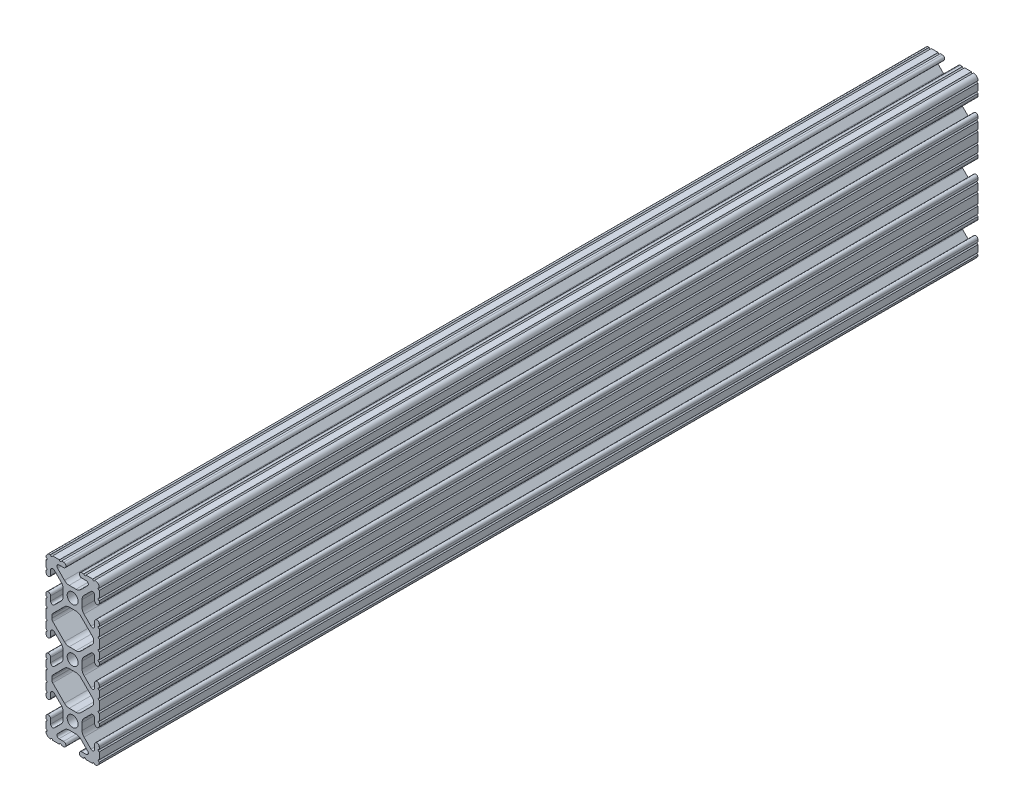
SolidWorks part; units mm, degrees
ref_plane "Front Plane" through (0, 0, 0) normal (0, 0, 1) x (1, 0, 0)
ref_plane "Top Plane" through (0, 0, 0) normal (0, 1, 0) x (1, 0, 0)
ref_plane "Right Plane" through (0, 0, 0) normal (1, 0, 0) x (0, 0, -1)
sketch "Sketch1" plane through (0, 0, 0) normal (0, 0, 1) x (1, 0, 0)
  line L0 (-9.9314, 12.1463) -> (-9.9314, 13.2537)
  line L1 (-9.4702, 14.3673) -> (-3.8759, 19.9616)
  line L2 (-1.6308, 20.8915) -> (1.6308, 20.8915)
  line L3 (3.8759, 19.9616) -> (9.4702, 14.3673)
  line L4 (9.9314, 13.2537) -> (9.9314, 12.1463)
  line L5 (9.4702, 11.0327) -> (3.8759, 5.4384)
  line L6 (1.6308, 4.5085) -> (-1.6308, 4.5085)
  line L7 (-3.8759, 5.4384) -> (-9.4702, 11.0327)
  line L8 (-9.9314, -13.2537) -> (-9.9314, -12.1463)
  line L9 (-9.4702, -11.0327) -> (-3.8759, -5.4384)
  line L10 (-1.6308, -4.5085) -> (1.6308, -4.5085)
  line L11 (3.8759, -5.4384) -> (9.4702, -11.0327)
  line L12 (9.9314, -12.1463) -> (9.9314, -13.2537)
  line L13 (9.4702, -14.3673) -> (3.8759, -19.9616)
  line L14 (1.6308, -20.8915) -> (-1.6308, -20.8915)
  line L15 (-3.8759, -19.9616) -> (-9.4702, -14.3673)
  line L16 (-6.3246, 38.1) -> (-9.5504, 38.1)
  line L17 (-12.7, 34.9504) -> (-12.7, 31.7246)
  line L18 (-12.7, 30.7086) -> (-12.7, 29.7023)
  line L19 (-10.4902, 29.7023) -> (-10.4902, 31.8748)
  line L20 (-8.7558, 32.5932) -> (-5.4384, 29.2759)
  line L21 (-4.5085, 27.0308) -> (-4.5085, 23.7692)
  line L22 (-5.4384, 21.5241) -> (-8.7558, 18.2068)
  line L23 (-10.4902, 18.9252) -> (-10.4902, 21.0977)
  line L24 (-12.7, 21.0977) -> (-12.7, 20.0914)
  line L25 (-12.7, 19.0754) -> (-12.7, 15.8496)
  line L26 (-12.7, 14.8336) -> (-12.7, 10.5664)
  line L27 (-12.7, 9.5504) -> (-12.7, 6.3246)
  line L28 (-12.7, 5.3086) -> (-12.7, 4.3023)
  line L29 (-10.4902, 4.3023) -> (-10.4902, 6.4748)
  line L30 (-8.7558, 7.1932) -> (-5.4384, 3.8759)
  line L31 (-4.5085, 1.6308) -> (-4.5085, -1.6308)
  line L32 (-5.4384, -3.8759) -> (-8.7558, -7.1932)
  line L33 (-10.4902, -6.4748) -> (-10.4902, -4.3023)
  line L34 (-12.7, -4.3023) -> (-12.7, -5.3086)
  line L35 (-12.7, -6.3246) -> (-12.7, -9.5504)
  line L36 (-12.7, -10.5664) -> (-12.7, -14.8336)
  line L37 (-12.7, -15.8496) -> (-12.7, -19.0754)
  line L38 (-12.7, -20.0914) -> (-12.7, -21.0977)
  line L39 (-10.4902, -21.0977) -> (-10.4902, -18.9252)
  line L40 (-8.7558, -18.2068) -> (-5.4384, -21.5241)
  line L41 (-4.5085, -23.7692) -> (-4.5085, -27.0308)
  line L42 (-5.4384, -29.2759) -> (-8.7558, -32.5932)
  line L43 (-10.4902, -31.8748) -> (-10.4902, -29.7023)
  line L44 (-12.7, -29.7023) -> (-12.7, -30.7086)
  line L45 (-12.7, -31.7246) -> (-12.7, -34.9504)
  line L46 (-9.5504, -38.1) -> (-6.3246, -38.1)
  line L47 (-5.3086, -38.1) -> (-4.3023, -38.1)
  line L48 (-4.3023, -35.8902) -> (-6.4748, -35.8902)
  line L49 (-7.1932, -34.1558) -> (-3.8759, -30.8384)
  line L50 (-1.6308, -29.9085) -> (1.6308, -29.9085)
  line L51 (3.8759, -30.8384) -> (7.1932, -34.1558)
  line L52 (6.4748, -35.8902) -> (4.3023, -35.8902)
  line L53 (4.3023, -38.1) -> (5.3086, -38.1)
  line L54 (6.3246, -38.1) -> (9.5504, -38.1)
  line L55 (12.7, -34.9504) -> (12.7, -31.7246)
  line L56 (12.7, -30.7086) -> (12.7, -29.7023)
  line L57 (10.4902, -29.7023) -> (10.4902, -31.8748)
  line L58 (8.7558, -32.5932) -> (5.4384, -29.2759)
  line L59 (4.5085, -27.0308) -> (4.5085, -23.7692)
  line L60 (5.4384, -21.5241) -> (8.7558, -18.2068)
  line L61 (10.4902, -18.9252) -> (10.4902, -21.0977)
  line L62 (12.7, -21.0977) -> (12.7, -20.0914)
  line L63 (12.7, -19.0754) -> (12.7, -15.8496)
  line L64 (12.7, -14.8336) -> (12.7, -10.5664)
  line L65 (12.7, -9.5504) -> (12.7, -6.3246)
  line L66 (12.7, -5.3086) -> (12.7, -4.3023)
  line L67 (10.4902, -4.3023) -> (10.4902, -6.4748)
  line L68 (8.7558, -7.1932) -> (5.4384, -3.8759)
  line L69 (4.5085, -1.6308) -> (4.5085, 1.6308)
  line L70 (5.4384, 3.8759) -> (8.7558, 7.1932)
  line L71 (10.4902, 6.4748) -> (10.4902, 4.3023)
  line L72 (12.7, 4.3023) -> (12.7, 5.3086)
  line L73 (12.7, 6.3246) -> (12.7, 9.5504)
  line L74 (12.7, 10.5664) -> (12.7, 14.8336)
  line L75 (12.7, 15.8496) -> (12.7, 19.0754)
  line L76 (12.7, 20.0914) -> (12.7, 21.0977)
  line L77 (10.4902, 21.0977) -> (10.4902, 18.9252)
  line L78 (8.7558, 18.2068) -> (5.4384, 21.5241)
  line L79 (4.5085, 23.7692) -> (4.5085, 27.0308)
  line L80 (5.4384, 29.2759) -> (8.7558, 32.5932)
  line L81 (10.4902, 31.8748) -> (10.4902, 29.7023)
  line L82 (12.7, 29.7023) -> (12.7, 30.7086)
  line L83 (12.7, 31.7246) -> (12.7, 34.9504)
  line L84 (9.5504, 38.1) -> (6.3246, 38.1)
  line L85 (5.3086, 38.1) -> (4.3023, 38.1)
  line L86 (4.3023, 35.8902) -> (6.4748, 35.8902)
  line L87 (7.1932, 34.1558) -> (3.8759, 30.8384)
  line L88 (1.6308, 29.9085) -> (-1.6308, 29.9085)
  line L89 (-3.8759, 30.8384) -> (-7.1932, 34.1558)
  line L90 (-6.4748, 35.8902) -> (-4.3023, 35.8902)
  line L91 (-4.3023, 38.1) -> (-5.3086, 38.1)
  circle A0 centre (0, 25.4) radius 2.6035
  arc A1 (-9.9314, 13.2537) -> (-9.4702, 14.3673) centre (-8.3566, 13.2537) cw
  arc A2 (-3.8759, 19.9616) -> (-1.6308, 20.8915) centre (-1.6308, 17.7165) cw
  arc A3 (1.6308, 20.8915) -> (3.8759, 19.9616) centre (1.6308, 17.7165) cw
  arc A4 (9.4702, 14.3673) -> (9.9314, 13.2537) centre (8.3566, 13.2537) cw
  arc A5 (9.9314, 12.1463) -> (9.4702, 11.0327) centre (8.3566, 12.1463) cw
  arc A6 (3.8759, 5.4384) -> (1.6308, 4.5085) centre (1.6308, 7.6835) cw
  arc A7 (-1.6308, 4.5085) -> (-3.8759, 5.4384) centre (-1.6308, 7.6835) cw
  arc A8 (-9.4702, 11.0327) -> (-9.9314, 12.1463) centre (-8.3566, 12.1463) cw
  arc A9 (-9.9314, -12.1463) -> (-9.4702, -11.0327) centre (-8.3566, -12.1463) cw
  arc A10 (-3.8759, -5.4384) -> (-1.6308, -4.5085) centre (-1.6308, -7.6835) cw
  arc A11 (1.6308, -4.5085) -> (3.8759, -5.4384) centre (1.6308, -7.6835) cw
  arc A12 (9.4702, -11.0327) -> (9.9314, -12.1463) centre (8.3566, -12.1463) cw
  arc A13 (9.9314, -13.2537) -> (9.4702, -14.3673) centre (8.3566, -13.2537) cw
  arc A14 (3.8759, -19.9616) -> (1.6308, -20.8915) centre (1.6308, -17.7165) cw
  arc A15 (-1.6308, -20.8915) -> (-3.8759, -19.9616) centre (-1.6308, -17.7165) cw
  arc A16 (-9.4702, -14.3673) -> (-9.9314, -13.2537) centre (-8.3566, -13.2537) cw
  circle A17 centre (0, -25.4) radius 2.6035
  circle A18 centre (0, 0) radius 2.6035
  arc A19 (-5.3086, 38.1) -> (-6.3246, 38.1) centre (-5.8166, 38.1) cw
  arc A20 (-9.5504, 38.1) -> (-10.5664, 38.1) centre (-10.0584, 38.1) cw
  arc A21 (-10.5664, 38.1) -> (-12.7, 35.9664) centre (-10.592, 35.992) ccw
  arc A22 (-12.7, 35.9664) -> (-12.7, 34.9504) centre (-12.7, 35.4584) cw
  arc A23 (-12.7, 31.7246) -> (-12.7, 30.7086) centre (-12.7, 31.2166) cw
  arc A24 (-12.7, 29.7023) -> (-10.4902, 29.7023) centre (-11.5951, 29.7023) ccw
  arc A25 (-10.4902, 31.8748) -> (-8.7558, 32.5932) centre (-9.4742, 31.8748) cw
  arc A26 (-5.4384, 29.2759) -> (-4.5085, 27.0308) centre (-7.6835, 27.0308) cw
  arc A27 (-4.5085, 23.7692) -> (-5.4384, 21.5241) centre (-7.6835, 23.7692) cw
  arc A28 (-8.7558, 18.2068) -> (-10.4902, 18.9252) centre (-9.4742, 18.9252) cw
  arc A29 (-10.4902, 21.0977) -> (-12.7, 21.0977) centre (-11.5951, 21.0977) ccw
  arc A30 (-12.7, 20.0914) -> (-12.7, 19.0754) centre (-12.7, 19.5834) cw
  arc A31 (-12.7, 15.8496) -> (-12.7, 14.8336) centre (-12.7, 15.3416) cw
  arc A32 (-12.7, 10.5664) -> (-12.7, 9.5504) centre (-12.7, 10.0584) cw
  arc A33 (-12.7, 6.3246) -> (-12.7, 5.3086) centre (-12.7, 5.8166) cw
  arc A34 (-12.7, 4.3023) -> (-10.4902, 4.3023) centre (-11.5951, 4.3023) ccw
  arc A35 (-10.4902, 6.4748) -> (-8.7558, 7.1932) centre (-9.4742, 6.4748) cw
  arc A36 (-5.4384, 3.8759) -> (-4.5085, 1.6308) centre (-7.6835, 1.6308) cw
  arc A37 (-4.5085, -1.6308) -> (-5.4384, -3.8759) centre (-7.6835, -1.6308) cw
  arc A38 (-8.7558, -7.1932) -> (-10.4902, -6.4748) centre (-9.4742, -6.4748) cw
  arc A39 (-10.4902, -4.3023) -> (-12.7, -4.3023) centre (-11.5951, -4.3023) ccw
  arc A40 (-12.7, -5.3086) -> (-12.7, -6.3246) centre (-12.7, -5.8166) cw
  arc A41 (-12.7, -9.5504) -> (-12.7, -10.5664) centre (-12.7, -10.0584) cw
  arc A42 (-12.7, -14.8336) -> (-12.7, -15.8496) centre (-12.7, -15.3416) cw
  arc A43 (-12.7, -19.0754) -> (-12.7, -20.0914) centre (-12.7, -19.5834) cw
  arc A44 (-12.7, -21.0977) -> (-10.4902, -21.0977) centre (-11.5951, -21.0977) ccw
  arc A45 (-10.4902, -18.9252) -> (-8.7558, -18.2068) centre (-9.4742, -18.9252) cw
  arc A46 (-5.4384, -21.5241) -> (-4.5085, -23.7692) centre (-7.6835, -23.7692) cw
  arc A47 (-4.5085, -27.0308) -> (-5.4384, -29.2759) centre (-7.6835, -27.0308) cw
  arc A48 (-8.7558, -32.5932) -> (-10.4902, -31.8748) centre (-9.4742, -31.8748) cw
  arc A49 (-10.4902, -29.7023) -> (-12.7, -29.7023) centre (-11.5951, -29.7023) ccw
  arc A50 (-12.7, -30.7086) -> (-12.7, -31.7246) centre (-12.7, -31.2166) cw
  arc A51 (-12.7, -34.9504) -> (-12.7, -35.9664) centre (-12.7, -35.4584) cw
  arc A52 (-12.7, -35.9664) -> (-10.5664, -38.1) centre (-10.592, -35.992) ccw
  arc A53 (-10.5664, -38.1) -> (-9.5504, -38.1) centre (-10.0584, -38.1) cw
  arc A54 (-6.3246, -38.1) -> (-5.3086, -38.1) centre (-5.8166, -38.1) cw
  arc A55 (-4.3023, -38.1) -> (-4.3023, -35.8902) centre (-4.3023, -36.9951) ccw
  arc A56 (-6.4748, -35.8902) -> (-7.1932, -34.1558) centre (-6.4748, -34.8742) cw
  arc A57 (-3.8759, -30.8384) -> (-1.6308, -29.9085) centre (-1.6308, -33.0835) cw
  arc A58 (1.6308, -29.9085) -> (3.8759, -30.8384) centre (1.6308, -33.0835) cw
  arc A59 (7.1932, -34.1558) -> (6.4748, -35.8902) centre (6.4748, -34.8742) cw
  arc A60 (4.3023, -35.8902) -> (4.3023, -38.1) centre (4.3023, -36.9951) ccw
  arc A61 (5.3086, -38.1) -> (6.3246, -38.1) centre (5.8166, -38.1) cw
  arc A62 (9.5504, -38.1) -> (10.5664, -38.1) centre (10.0584, -38.1) cw
  arc A63 (10.5664, -38.1) -> (12.7, -35.9664) centre (10.592, -35.992) ccw
  arc A64 (12.7, -35.9664) -> (12.7, -34.9504) centre (12.7, -35.4584) cw
  arc A65 (12.7, -31.7246) -> (12.7, -30.7086) centre (12.7, -31.2166) cw
  arc A66 (12.7, -29.7023) -> (10.4902, -29.7023) centre (11.5951, -29.7023) ccw
  arc A67 (10.4902, -31.8748) -> (8.7558, -32.5932) centre (9.4742, -31.8748) cw
  arc A68 (5.4384, -29.2759) -> (4.5085, -27.0308) centre (7.6835, -27.0308) cw
  arc A69 (4.5085, -23.7692) -> (5.4384, -21.5241) centre (7.6835, -23.7692) cw
  arc A70 (8.7558, -18.2068) -> (10.4902, -18.9252) centre (9.4742, -18.9252) cw
  arc A71 (10.4902, -21.0977) -> (12.7, -21.0977) centre (11.5951, -21.0977) ccw
  arc A72 (12.7, -20.0914) -> (12.7, -19.0754) centre (12.7, -19.5834) cw
  arc A73 (12.7, -15.8496) -> (12.7, -14.8336) centre (12.7, -15.3416) cw
  arc A74 (12.7, -10.5664) -> (12.7, -9.5504) centre (12.7, -10.0584) cw
  arc A75 (12.7, -6.3246) -> (12.7, -5.3086) centre (12.7, -5.8166) cw
  arc A76 (12.7, -4.3023) -> (10.4902, -4.3023) centre (11.5951, -4.3023) ccw
  arc A77 (10.4902, -6.4748) -> (8.7558, -7.1932) centre (9.4742, -6.4748) cw
  arc A78 (5.4384, -3.8759) -> (4.5085, -1.6308) centre (7.6835, -1.6308) cw
  arc A79 (4.5085, 1.6308) -> (5.4384, 3.8759) centre (7.6835, 1.6308) cw
  arc A80 (8.7558, 7.1932) -> (10.4902, 6.4748) centre (9.4742, 6.4748) cw
  arc A81 (10.4902, 4.3023) -> (12.7, 4.3023) centre (11.5951, 4.3023) ccw
  arc A82 (12.7, 5.3086) -> (12.7, 6.3246) centre (12.7, 5.8166) cw
  arc A83 (12.7, 9.5504) -> (12.7, 10.5664) centre (12.7, 10.0584) cw
  arc A84 (12.7, 14.8336) -> (12.7, 15.8496) centre (12.7, 15.3416) cw
  arc A85 (12.7, 19.0754) -> (12.7, 20.0914) centre (12.7, 19.5834) cw
  arc A86 (12.7, 21.0977) -> (10.4902, 21.0977) centre (11.5951, 21.0977) ccw
  arc A87 (10.4902, 18.9252) -> (8.7558, 18.2068) centre (9.4742, 18.9252) cw
  arc A88 (5.4384, 21.5241) -> (4.5085, 23.7692) centre (7.6835, 23.7692) cw
  arc A89 (4.5085, 27.0308) -> (5.4384, 29.2759) centre (7.6835, 27.0308) cw
  arc A90 (8.7558, 32.5932) -> (10.4902, 31.8748) centre (9.4742, 31.8748) cw
  arc A91 (10.4902, 29.7023) -> (12.7, 29.7023) centre (11.5951, 29.7023) ccw
  arc A92 (12.7, 30.7086) -> (12.7, 31.7246) centre (12.7, 31.2166) cw
  arc A93 (12.7, 34.9504) -> (12.7, 35.9664) centre (12.7, 35.4584) cw
  arc A94 (12.7, 35.9664) -> (10.5664, 38.1) centre (10.592, 35.992) ccw
  arc A95 (10.5664, 38.1) -> (9.5504, 38.1) centre (10.0584, 38.1) cw
  arc A96 (6.3246, 38.1) -> (5.3086, 38.1) centre (5.8166, 38.1) cw
  arc A97 (4.3023, 38.1) -> (4.3023, 35.8902) centre (4.3023, 36.9951) ccw
  arc A98 (6.4748, 35.8902) -> (7.1932, 34.1558) centre (6.4748, 34.8742) cw
  arc A99 (3.8759, 30.8384) -> (1.6308, 29.9085) centre (1.6308, 33.0835) cw
  arc A100 (-1.6308, 29.9085) -> (-3.8759, 30.8384) centre (-1.6308, 33.0835) cw
  arc A101 (-7.1932, 34.1558) -> (-6.4748, 35.8902) centre (-6.4748, 34.8742) cw
  arc A102 (-4.3023, 35.8902) -> (-4.3023, 38.1) centre (-4.3023, 36.9951) ccw
extrude "Boss-Extrude1" add sketch "Sketch1" against normal blind 419.1
